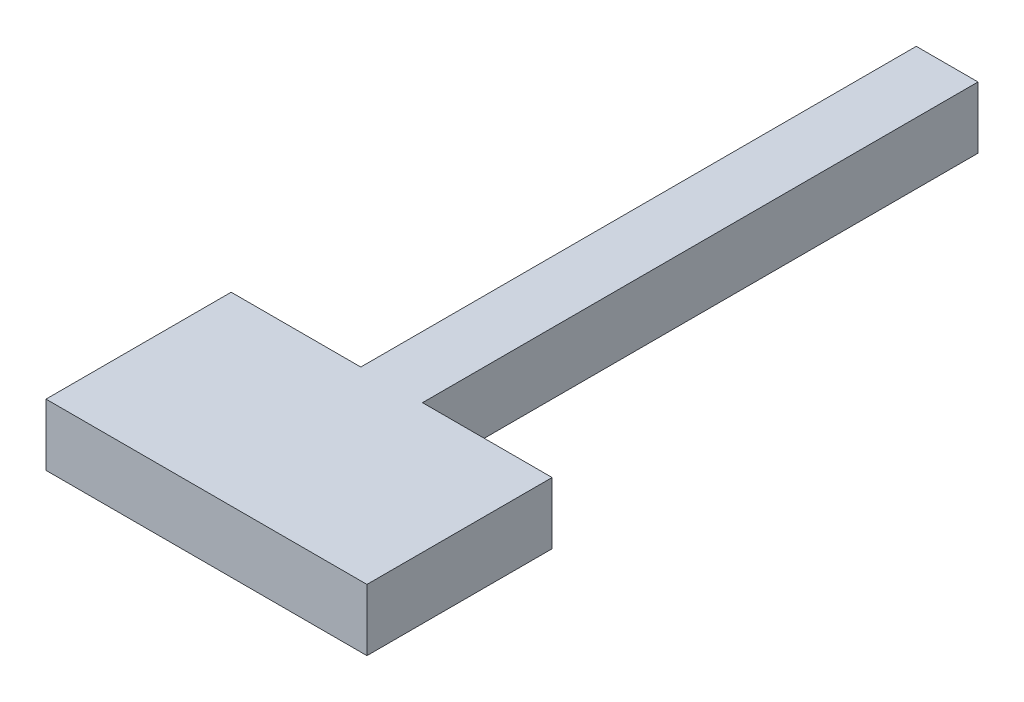
SolidWorks part; units mm, degrees
ref_plane "Front Plane" through (0, 0, 0) normal (0, 0, 1) x (1, 0, 0)
ref_plane "Top Plane" through (0, 0, 0) normal (0, 1, 0) x (1, 0, 0)
ref_plane "Right Plane" through (0, 0, 0) normal (1, 0, 0) x (0, 0, -1)
sketch "Sketch1" plane through (0, 0, 0) normal (0, 0, 1) x (1, 0, 0)
  line L1 (-27.3518, 2.7213) -> (-22.3518, 2.7213)
  line L2 (-27.3518, 2.7213) -> (-27.3518, 7.7213)
  line L3 (-27.3518, 7.7213) -> (-22.3518, 7.7213)
  line L4 (-22.3518, 2.7213) -> (-22.3518, 7.7213)
  dimension "D1" = 5
  dimension "D2" = 5
extrude "Boss-Extrude1" add sketch "Sketch1" along normal blind 45
sketch "Sketch2" plane through (0, 0, 45) normal (0, 0, 1) x (1, 0, 0)
  line L0 (-27.3518, 7.7213) -> (-27.3518, 2.7213) construction
  line L1 (-37.8518, 2.7213) -> (-11.8518, 2.7213)
  line L2 (-37.8518, 2.7213) -> (-37.8518, 7.7213)
  line L3 (-37.8518, 7.7213) -> (-11.8518, 7.7213)
  line L4 (-11.8518, 2.7213) -> (-11.8518, 7.7213)
  line L5 (-37.8518, 2.7213) -> (-11.8518, 7.7213) construction
  line L6 (-37.8518, 7.7213) -> (-11.8518, 2.7213) construction
  point P0 (-24.8518, 5.2213)
  dimension "D1" = 26
  dimension "D2" = 2.5
extrude "Boss-Extrude2" add sketch "Sketch2" along normal blind 15
sketch "Sketch3" plane through (0, 0, 0) normal (0, 0, -1) x (-1, 0, 0)
  circle A0 centre (24.8518, 5.2213) radius 1.5
extrude "Cut-Extrude1" cut sketch "Sketch3" against normal blind 5
